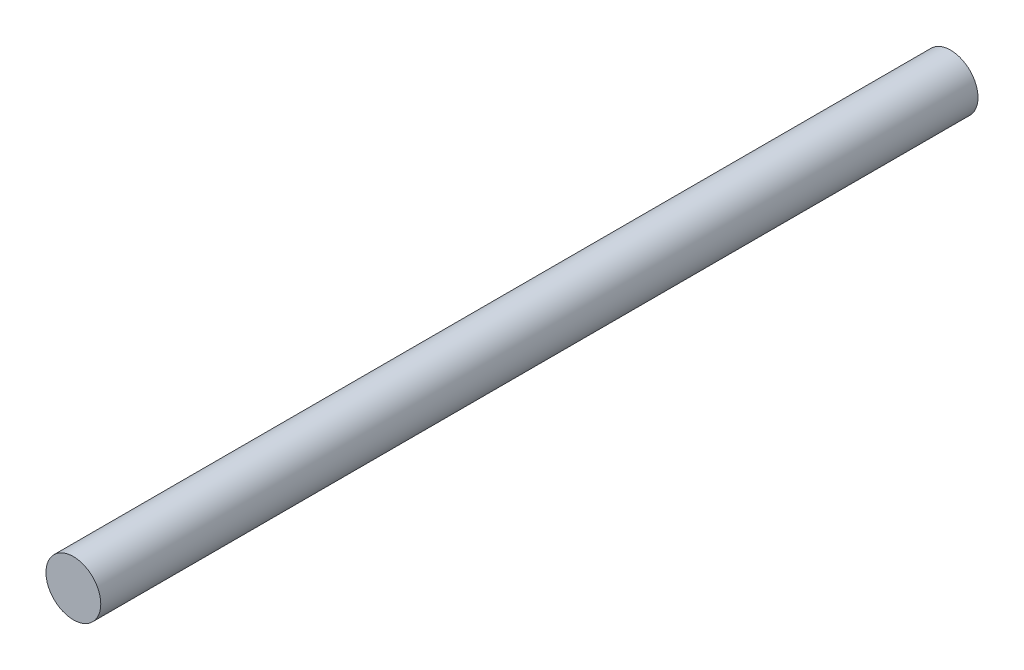
SolidWorks part; units mm, degrees
ref_plane "Front Plane" through (0, 0, 0) normal (0, 0, 1) x (1, 0, 0)
ref_plane "Top Plane" through (0, 0, 0) normal (0, 1, 0) x (1, 0, 0)
ref_plane "Right Plane" through (0, 0, 0) normal (1, 0, 0) x (0, 0, -1)
sketch "Sketch1" plane through (0, 0, 0) normal (0, 0, 1) x (1, 0, 0)
  circle A0 centre (0, 0) radius 3.175
  dimension "D1" = 6.35
extrude "Boss-Extrude1" add sketch "Sketch1" along normal blind 101.6
